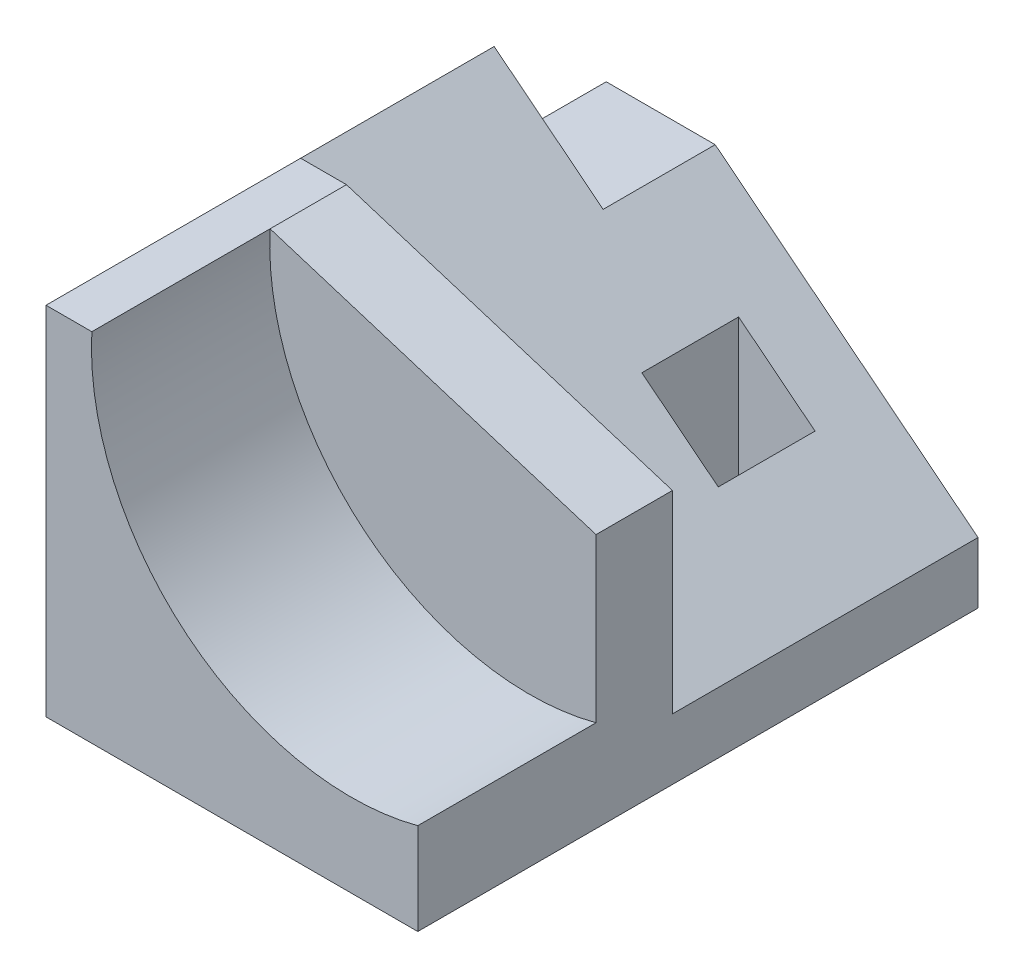
SolidWorks part; units mm, degrees
ref_plane "Front Plane" through (0, 0, 0) normal (0, 0, 1) x (1, 0, 0)
ref_plane "Top Plane" through (0, 0, 0) normal (0, 1, 0) x (1, 0, 0)
ref_plane "Right Plane" through (0, 0, 0) normal (1, 0, 0) x (0, 0, -1)
sketch "Sketch1" plane through (0, 0, 0) normal (0, 1, 0) x (1, 0, 0)
  line L1 (-18.25, -27.5) -> (18.25, -27.5)
  line L2 (-18.25, -27.5) -> (-18.25, 27.5)
  line L3 (-18.25, 27.5) -> (18.25, 27.5)
  line L4 (18.25, -27.5) -> (18.25, 27.5)
  line L5 (-18.25, -27.5) -> (18.25, 27.5) construction
  line L6 (-18.25, 27.5) -> (18.25, -27.5) construction
  line L7 (1.25, 21) -> (8.75, 21)
  line L8 (1.25, 21) -> (1.25, 11.5)
  line L9 (1.25, 11.5) -> (8.75, 11.5)
  line L10 (8.75, 21) -> (8.75, 11.5)
  point P0 (0, 0)
  dimension "D1" = 36.5
  dimension "D2" = 55
  dimension "D3" = 9.5
  dimension "D4" = 7.5
  dimension "D5" = 6.5
  dimension "D6" = 9.5
extrude "Boss-Extrude1" add sketch "Sketch1" along normal blind 35
sketch "Sketch3" plane through (0, 35, 0) normal (0, 1, 0) x (1, 0, 0)
  line L1 (-18.25, 27.5) -> (-7.25, 27.5)
  line L2 (-18.25, 27.5) -> (-18.25, 16.5)
  line L3 (-18.25, 16.5) -> (-7.25, 16.5)
  line L4 (-7.25, 27.5) -> (-7.25, 16.5)
  dimension "D1" = 11
extrude "Cut-Extrude2" cut sketch "Sketch3" against normal blind 8.5
sketch "Sketch2" plane through (0, 0, -27.5) normal (0, 0, -1) x (-1, 0, 0)
  line L0 (18.25, 35) -> (-18.25, 6)
  line L6 (-18.25, 0) -> (18.25, 0)
  line L12 (-18.25, 35) -> (-18.25, 0)
  line L13 (18.25, 35) -> (-18.25, 35)
  line L14 (18.25, 0) -> (18.25, 35)
  line L19 (-18.25, 0) -> (18.25, 0)
  line L20 (-18.25, 35) -> (-18.25, 0)
  line L21 (18.25, 35) -> (-18.25, 35)
  line L22 (18.25, 0) -> (18.25, 35)
  line M7 (7.25, 35) -> (-18.25, 35)
  line M8 (-18.25, 35) -> (-18.25, 0)
  line M14 (18.25, 26.5) -> (7.25, 26.5)
  line M15 (7.25, 26.5) -> (7.25, 35)
  dimension "D2" = 6
  dimension "D1" = 0
extrude "Cut-Extrude1" cut sketch "Sketch2" against normal blind 30 contours L0 L21 M15 M14 | L0 M14 M15 M7 M8
sketch "Sketch4" plane through (0, 0, 27.5) normal (0, 0, 1) x (1, 0, 0)
  line L0 (-13.75, 35) -> (-13.75, 0) construction
  line L4 (-18.25, 0) -> (18.25, 0)
  line L5 (18.25, 0) -> (18.25, 35)
  line L6 (18.25, 35) -> (-18.25, 35)
  line L7 (-18.25, 35) -> (-18.25, 0)
  line L8 (-18.25, 0) -> (18.25, 0)
  line L9 (18.25, 0) -> (18.25, 35)
  line L10 (18.25, 35) -> (-18.25, 35)
  line L11 (-18.25, 35) -> (-18.25, 0)
  arc A0 (-13.75, 35) -> (18.25, 9) centre (11.7141, 33.6482) ccw
  line M7 (18.25, 35) -> (-18.25, 35)
  dimension "D3" = 9
  dimension "D4" = 25.5
  dimension "D2" = 4.5
  dimension "D1" = 0
extrude "Cut-Extrude3" cut sketch "Sketch4" against normal blind 17.5 contours L0 A0 L9 M7 | L0 A0
sketch "Sketch5" plane through (0, 0, 10) normal (0, 0, 1) x (1, 0, 0)
  line L0 (-13.75, 35) -> (18.25, 25)
  line L1 (-18.25, 0) -> (18.25, 0) construction
  line L2 (18.25, 35) -> (-13.75, 35)
  line L3 (18.25, 9) -> (18.25, 35)
  line L4 (18.25, 35) -> (-13.75, 35)
  line L5 (18.25, 9) -> (18.25, 35)
  arc A1 (-13.75, 35) -> (18.25, 9) centre (11.7141, 33.6482) ccw
  arc A2 (-13.75, 35) -> (18.25, 9) centre (11.7141, 33.6482) ccw
  line M4 (18.25, 35) -> (-13.75, 35)
  line M6 (18.25, 9) -> (18.25, 35)
  dimension "D2" = 25
  dimension "D1" = 0
extrude "Cut-Extrude4" cut sketch "Sketch5" against normal up to next contours L0 M4 M6
